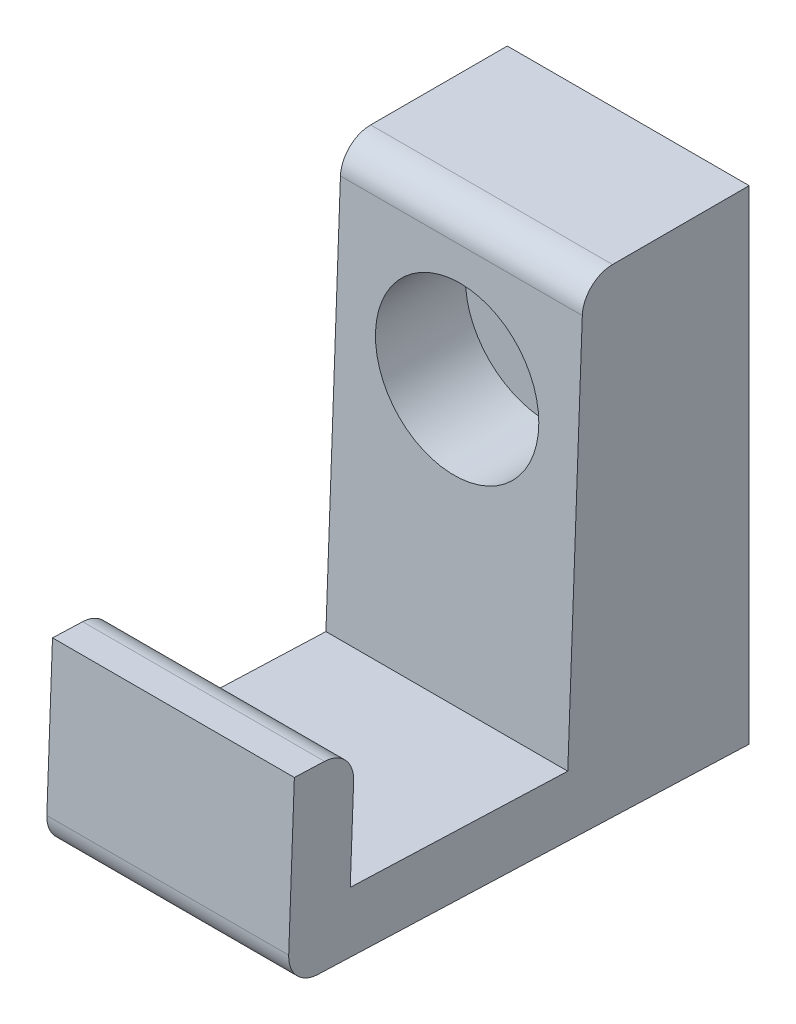
SolidWorks part; units mm, degrees
ref_plane "Front Plane" through (0, 0, 0) normal (0, 0, 1) x (1, 0, 0)
ref_plane "Top Plane" through (0, 0, 0) normal (0, 1, 0) x (1, 0, 0)
ref_plane "Right Plane" through (0, 0, 0) normal (1, 0, 0) x (0, 0, -1)
sketch "Sketch4" plane through (0, 0, 0) normal (1, 0, 0) x (0, 0, -1)
  line L0 (0, 0) -> (0, 40)
  line L1 (0, 40) -> (-13.708, 40)
  line L2 (-13.708, 40) -> (-15, 5.5663)
  line L3 (-15, 5.5663) -> (-32.9873, 6.2413)
  line L4 (-32.9873, 6.2413) -> (-32.6124, 16.2342)
  line L5 (-32.6124, 16.2342) -> (-37.6089, 16.4217)
  line L6 (-37.6089, 16.4217) -> (-38.1713, 1.4323)
  line L7 (-38.1713, 1.4323) -> (0, 0)
  line L8 (-15, 5.5663) -> (0, 405.335) construction
  line L9 (0, 405.335) -> (-17.9873, 406.0099) construction
  line L10 (-17.9873, 406.0099) -> (-32.9873, 6.2413) construction
  point P3 (11.6408, 402.7681)
  point P13 (-8.3622, 53.6905)
  point P14 (0, 0)
  point P15 (-35.1106, 16.328)
  dimension "D1" = 5
  dimension "D2" = 5
  dimension "D3" = 18
  dimension "D4" = 15
  dimension "D5" = 400.05
  dimension "D6" = 15
  dimension "D7" = 40
extrude "Boss-Extrude1" add sketch "Sketch4" along normal mid plane 20
ref_plane "Plane1" through (0, 0, 13.708) normal (0, 0, 1) x (1, 0, 0)
sketch "Sketch5" plane through (0, 0, 13.708) normal (0, 0, 1) x (1, 0, 0)
  line L0 (0, 16.4217) -> (0, 40) construction
  line L1 (10, 16.4217) -> (-10, 16.4217) construction
  line L2 (10, 40) -> (-10, 40) construction
  circle A0 centre (0, 28.2109) radius 6.75
  point P8 (1.9689, 28.2554)
  point P9 (2.0898, 28.3763)
  point P10 (0, 28.2109)
  dimension "D1" = 13.5
extrude "Cut-Extrude1" cut sketch "Sketch5" against normal blind 7 and the other way up to next
sketch "Sketch6" plane through (0, 0, 6.708) normal (0, 0, 1) x (1, 0, 0)
  line L0 (0, 21.4609) -> (0, 34.9609) construction
  circle A0 centre (0, 28.2109) radius 2.5
  circle A1 centre (0, 28.2109) radius 6.75 construction
  circle A2 centre (0, 28.2109) radius 6.75 construction
  point P9 (0, 28.2109)
  dimension "D1" = 5
extrude "Cut-Extrude2" cut sketch "Sketch6" against normal up to next
fillet "Fillet1" radius 2.5 3 edges at (0, 1.4323, 38.1713) (0, 40, 13.708) (0, 16.2342, 32.6124)
